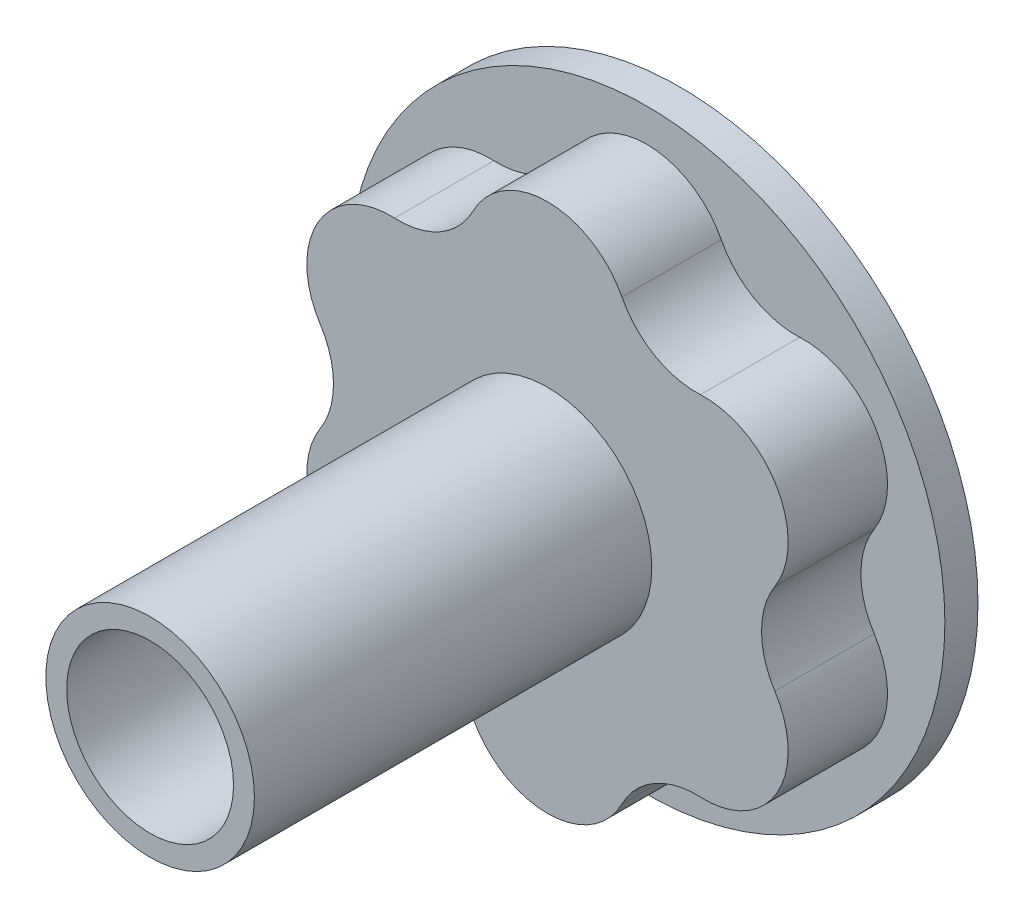
SolidWorks part; units mm, degrees
material "ABS"
ref_plane "Front Plane" through (0, 0, 0) normal (0, 0, 1) x (1, 0, 0)
ref_plane "Top Plane" through (0, 0, 0) normal (0, 1, 0) x (1, 0, 0)
ref_plane "Right Plane" through (0, 0, 0) normal (1, 0, 0) x (0, 0, -1)
sketch "Sketch1" plane through (0, 0, 0) normal (0, 0, 1) x (1, 0, 0)
  circle A0 centre (0, 0) radius 11.1125 construction
  circle A1 centre (0, 0) radius 12.7 construction
  circle A2 centre (0, 0) radius 3
  arc A3 (-3.5686, 10.5239) -> (3.5686, 10.5239) centre (0, 8.6859) cw
  arc A4 (3.5686, 10.5239) -> (7.3297, 8.3524) centre (7.1372, 12.362) ccw
  arc A5 (7.3297, 8.3524) -> (10.8983, 2.1715) centre (7.5222, 4.3429) cw
  arc A6 (10.8983, 2.1715) -> (10.8983, -2.1715) centre (14.2744, 0) ccw
  arc A7 (10.8983, -2.1715) -> (7.3297, -8.3524) centre (7.5222, -4.3429) cw
  arc A8 (7.3297, -8.3524) -> (3.5686, -10.5239) centre (7.1372, -12.362) ccw
  arc A9 (3.5686, -10.5239) -> (-3.5686, -10.5239) centre (0, -8.6859) cw
  arc A10 (-3.5686, -10.5239) -> (-7.3297, -8.3524) centre (-7.1372, -12.362) ccw
  arc A11 (-7.3297, -8.3524) -> (-10.8983, -2.1715) centre (-7.5222, -4.3429) cw
  arc A12 (-10.8983, -2.1715) -> (-10.8983, 2.1715) centre (-14.2744, 0) ccw
  arc A13 (-10.8983, 2.1715) -> (-7.3297, 8.3524) centre (-7.5222, 4.3429) cw
  arc A14 (-7.3297, 8.3524) -> (-3.5686, 10.5239) centre (-7.1372, 12.362) ccw
  dimension "D1" = 25.4
  dimension "D2" = 1.5875
  dimension "D3" = 6
extrude "Boss-Extrude1" add sketch "Sketch1" along normal blind 4.7625
sketch "Sketch2" plane through (0, 0, 0) normal (0, 0, -1) x (-1, 0, 0)
  circle A0 centre (0, 0) radius 14.2875
  circle A1 centre (0, 0) radius 3
  circle A2 centre (0, 0) radius 3 construction
  dimension "D1" = 28.575
extrude "Boss-Extrude2" add sketch "Sketch2" along normal blind 1.5875
sketch "Sketch3" plane through (0, 0, 4.7625) normal (0, 0, 1) x (1, 0, 0)
  circle A0 centre (0, 0) radius 5
  circle A1 centre (0, 0) radius 3 construction
  circle A2 centre (0, 0) radius 3
  dimension "D1" = 10
extrude "Boss-Extrude3" add sketch "Sketch3" along normal blind 19.05
sketch "Sketch4" plane through (0, 0, 23.8125) normal (0, 0, 1) x (1, 0, 0)
  circle A0 centre (0, 0) radius 4
  dimension "D1" = 8
extrude "Cut-Extrude1" cut sketch "Sketch4" against normal blind 9.525
